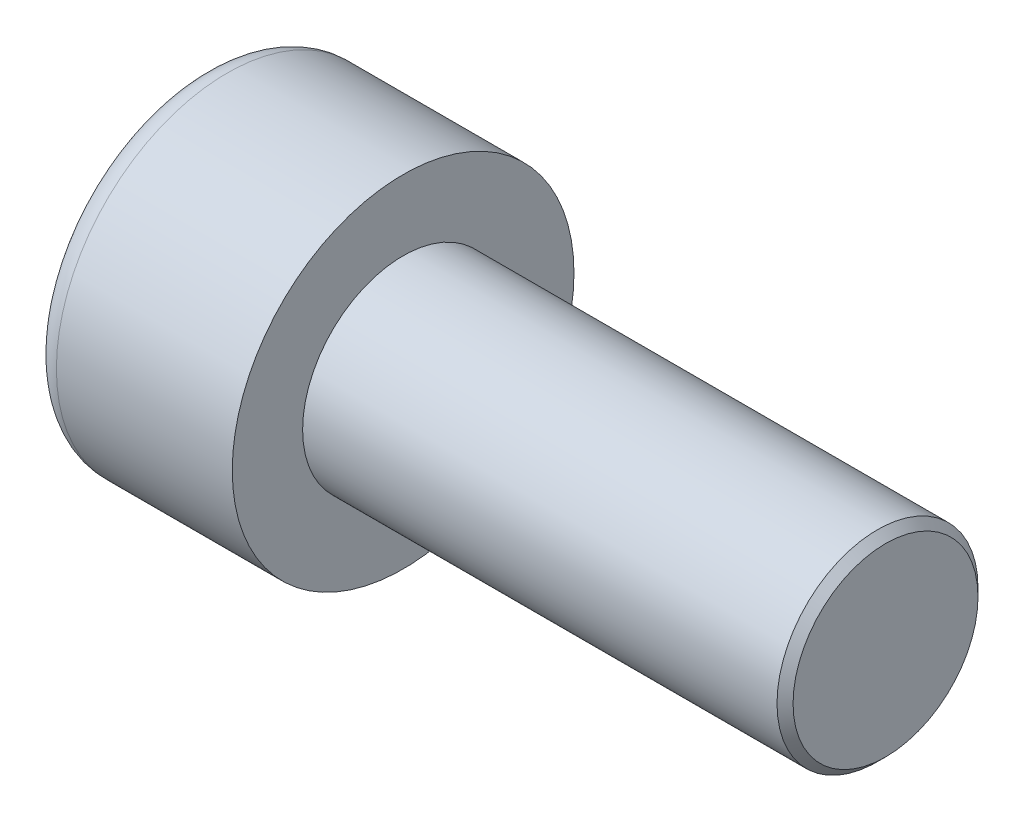
SolidWorks part; units mm, degrees
ref_plane "Front" through (0, 0, 0) normal (0, 0, 1) x (1, 0, 0)
ref_plane "Top" through (0, 0, 0) normal (0, 1, 0) x (1, 0, 0)
ref_plane "Right" through (0, 0, 0) normal (1, 0, 0) x (0, 0, -1)
sketch "Sketch1" plane through (0, 0, 0) normal (1, 0, 0) x (0, 0, -1)
  circle A0 centre (0, 0) radius 4.25
  dimension "dk" = 8.5
extrude "BaseHead" add sketch "Sketch1" along normal blind 5
sketch "Sketch2" plane through (5, 0, 0) normal (1, 0, 0) x (0, 0, -1)
  circle A0 centre (0, 0) radius 2.5
  dimension "d" = 5
extrude "BaseBody" add sketch "Sketch2" along normal blind 12
cosmetic thread "ThreadCosmetic1" parameters "b"=12, "D2"=4.134
sketch "Sketch3" plane through (0, 0, 0) normal (1, 0, 0) x (0, 0, -1)
  line L1 (2.3094, 0) -> (1.1547, 2)
  line L2 (1.1547, 2) -> (-1.1547, 2)
  line L3 (-1.1547, 2) -> (-2.3094, 0)
  line L4 (-2.3094, 0) -> (-1.1547, -2)
  line L5 (-1.1547, -2) -> (1.1547, -2)
  line L6 (1.1547, -2) -> (2.3094, 0)
  circle A0 centre (0, 0) radius 2 construction
  dimension "s" = 4
  dimension "e" = 4.6188
extrude "HexagonSocket" cut sketch "Sketch3" along normal blind 2.5
sketch "Sketch4" plane through (-4.1961, 0.75, 0) normal (0, 0, 1) x (-1, 0, 0)
  line L0 (-6.6961, 2.75) -> (-7.8508, 0.75)
  line L2 (-7.8508, 0.75) -> (-6.6961, 0.75)
  line L3 (-6.6961, 0.75) -> (-6.6961, 2.75)
  line L4 (-5.0351, 0.75) -> (0.839, 0.75) construction
  line L5 (-21.1961, 0.75) -> (-9.1961, 0.75) construction
  line L6 (-9.1961, 0.75) -> (-4.1961, 0.75) construction
  dimension "m" = 60
revolve "Cut-Revolve1" cut sketch "Sketch4" angle 360 about L4
fillet "HeadFillet" [suppressed] radius 0.2
fillet "TopFillet" radius 0.625 1 edges at (0, 0, -4.25)
chamfer "Chamfer1" distance 0.2 angle 45 1 edges at (17, 0, -2.5)
sketch "Sketch5" plane through (0, 0, 0) normal (0, 0, 1) x (1, 0, 0)
  line L0 (16.8, 2.125) -> (17.0165, 2.5)
  line L1 (17.0165, 2.5) -> (17.0165, 2.933)
  line L2 (17.0165, 2.933) -> (16.5835, 2.933)
  line L3 (16.5835, 2.933) -> (16.5835, 2.5)
  line L4 (16.5835, 2.5) -> (16.8, 2.125)
  line L5 (0, 0) -> (7.8886, 0) construction
  line L6 (16.8, -2.5) -> (16.8, 2.5) construction
  dimension "D1" = 5
  dimension "D2" = 0.433
revolve "Cut-Revolve10" [suppressed] cut sketch "Sketch5" angle 360 about L5
pattern_linear "LPattern10" [suppressed] count 23 spacing 0.5196 along (1, 0, 0)
equation "\"r1@TopFillet\" = \"d@Sketch2\" / 8"
equation "\"D1@Chamfer1\" = \"r@HeadFillet\""
equation "\"D1@Sketch5\" = \"d@Sketch2\""
equation "\"D2@Sketch5\" =  ( \"d@Sketch2\" - \"D2@ThreadCosmetic1\" )  / 2"
equation "\"D3@LPattern10\" = \"D2@Sketch5\" * 1.2"
equation "\"D1@LPattern10\" = \"b@ThreadCosmetic1\" / \"D3@LPattern10\""
